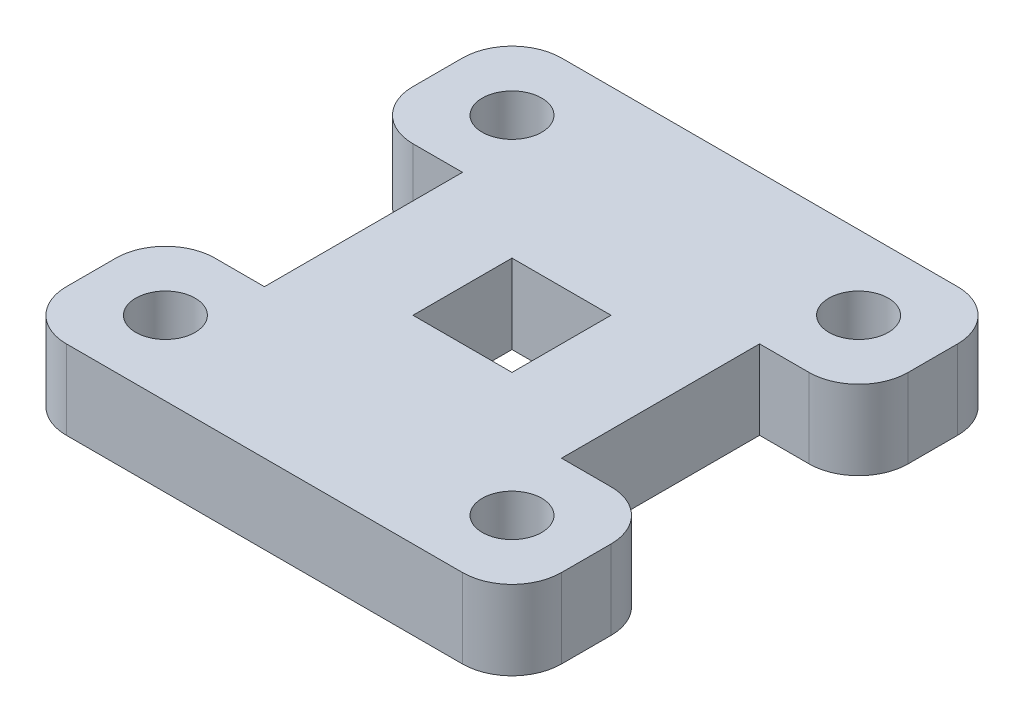
SolidWorks part; units mm, degrees
ref_plane "Front Plane" through (0, 0, 0) normal (0, 0, 1) x (1, 0, 0)
ref_plane "Top Plane" through (0, 0, 0) normal (0, 1, 0) x (1, 0, 0)
ref_plane "Right Plane" through (0, 0, 0) normal (1, 0, 0) x (0, 0, -1)
sketch "Sketch1" plane through (0, 0, 0) normal (0, 1, 0) x (1, 0, 0)
  line L0 (0, -50) -> (0, 50) construction
  line L5 (-40, 50) -> (40, 50)
  line L6 (50, 40) -> (50, 30)
  line L7 (40, 20) -> (30, 20)
  line L8 (30, 20) -> (30, -20)
  line L9 (30, 0) -> (-30, 0) construction
  line L10 (40, -20) -> (30, -20)
  line L11 (50, -40) -> (50, -30)
  line L12 (-40, -50) -> (40, -50)
  line L13 (-50, -40) -> (-50, -30)
  line L14 (-40, -20) -> (-30, -20)
  line L15 (-30, 20) -> (-30, -20)
  line L16 (-40, 20) -> (-30, 20)
  line L17 (-50, 40) -> (-50, 30)
  line L19 (-10, -10) -> (10, -10)
  line L20 (-10, -10) -> (-10, 10)
  line L21 (-10, 10) -> (10, 10)
  line L22 (10, -10) -> (10, 10)
  line L23 (-10, -10) -> (10, 10) construction
  line L24 (-10, 10) -> (10, -10) construction
  circle A0 centre (35, 35) radius 6
  arc A1 (50, 30) -> (40, 20) centre (40, 30) cw
  arc A2 (40, 50) -> (50, 40) centre (40, 40) cw
  arc A3 (40, -50) -> (50, -40) centre (40, -40) ccw
  arc A4 (50, -30) -> (40, -20) centre (40, -30) ccw
  circle A5 centre (35, -35) radius 6
  circle A6 centre (-35, -35) radius 6
  arc A7 (-50, -30) -> (-40, -20) centre (-40, -30) cw
  arc A8 (-40, -50) -> (-50, -40) centre (-40, -40) cw
  arc A9 (-40, 50) -> (-50, 40) centre (-40, 40) ccw
  arc A10 (-50, 30) -> (-40, 20) centre (-40, 30) ccw
  circle A11 centre (-35, 35) radius 6
  point P8 (0, 0)
  point P12 (50, 20)
  point P15 (50, 50)
  point P26 (50, -50)
  point P27 (50, -20)
  point P46 (0, 0)
  point P47 (-50, -20)
  point P48 (-50, -50)
  point P49 (-50, 50)
  point P50 (-50, 20)
  dimension "D7" = 12
  dimension "D8" = 10
  dimension "D1" = 50
  dimension "D2" = 20
  dimension "D3" = 50
  dimension "D4" = 20
  dimension "D5" = 35
  dimension "D6" = 35
  dimension "D9" = 20
  dimension "D10" = 20
extrude "Boss-Extrude1" add sketch "Sketch1" along normal blind 16
